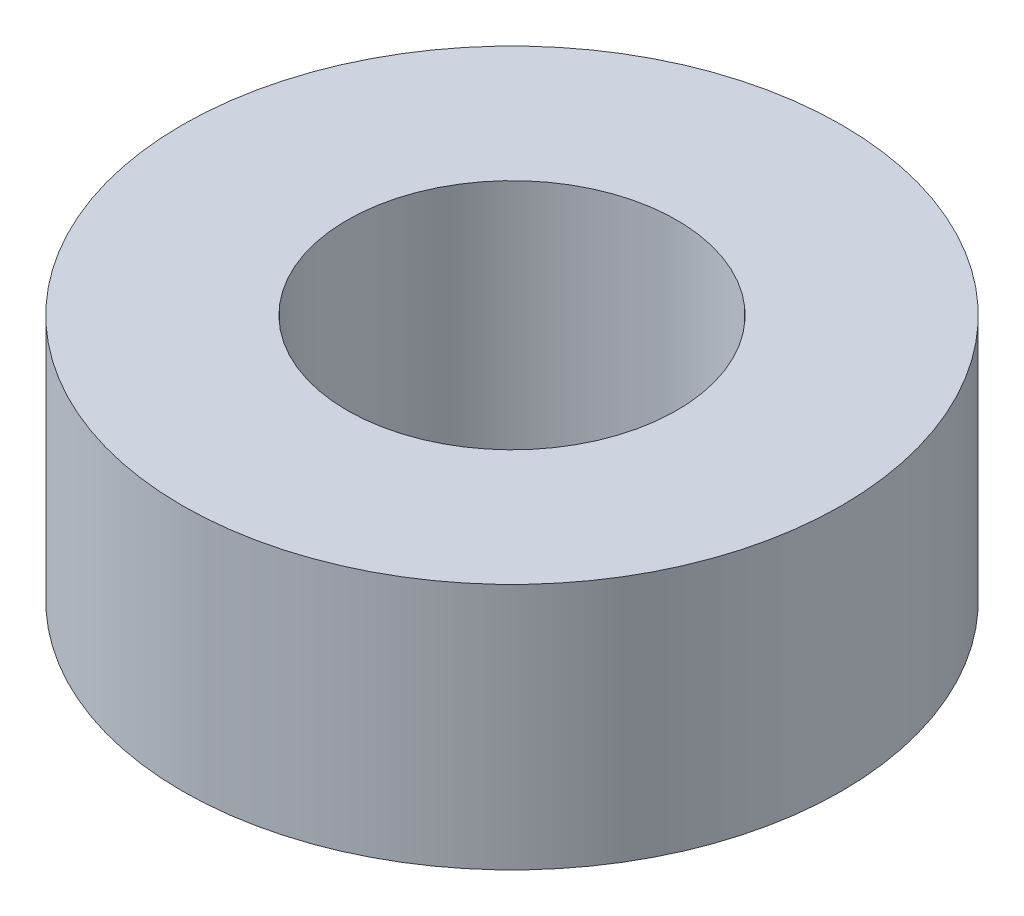
SolidWorks part; units mm, degrees
ref_plane "Front Plane" through (0, 0, 0) normal (0, 0, 1) x (1, 0, 0)
ref_plane "Top Plane" through (0, 0, 0) normal (0, 1, 0) x (1, 0, 0)
ref_plane "Right Plane" through (0, 0, 0) normal (1, 0, 0) x (0, 0, -1)
sketch "Sketch1" plane through (0, 0, 0) normal (0, 1, 0) x (1, 0, 0)
  circle A0 centre (0, 0) radius 2
  circle A1 centre (0, 0) radius 4
  dimension "D1" = 4
  dimension "D2" = 8
extrude "Boss-Extrude1" add sketch "Sketch1" along normal blind 3
